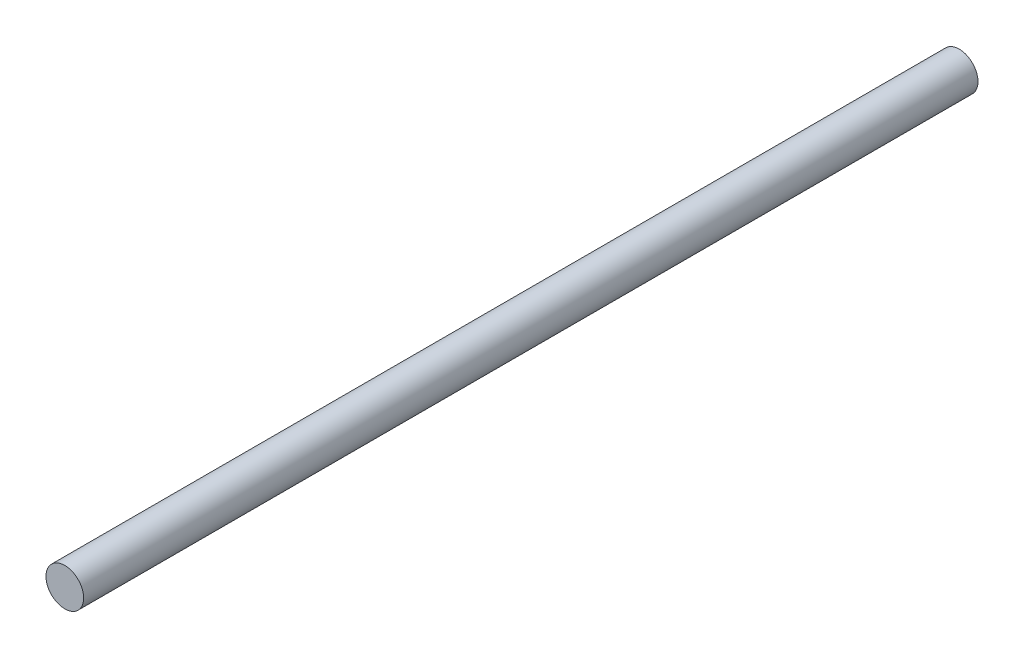
SolidWorks part; units mm, degrees
ref_plane "正面" through (0, 0, 0) normal (0, 0, 1) x (1, 0, 0)
ref_plane "平面" through (0, 0, 0) normal (0, 1, 0) x (1, 0, 0)
ref_plane "右側面" through (0, 0, 0) normal (1, 0, 0) x (0, 0, -1)
sketch "ｽｹｯﾁ2" plane through (0, 0, 12) normal (0, 0, 1) x (1, 0, 0)
  circle A1 centre (0, 62.5) radius 4
extrude "ﾎﾞｽ - 押し出し2" add sketch "ｽｹｯﾁ2" along normal blind 190
